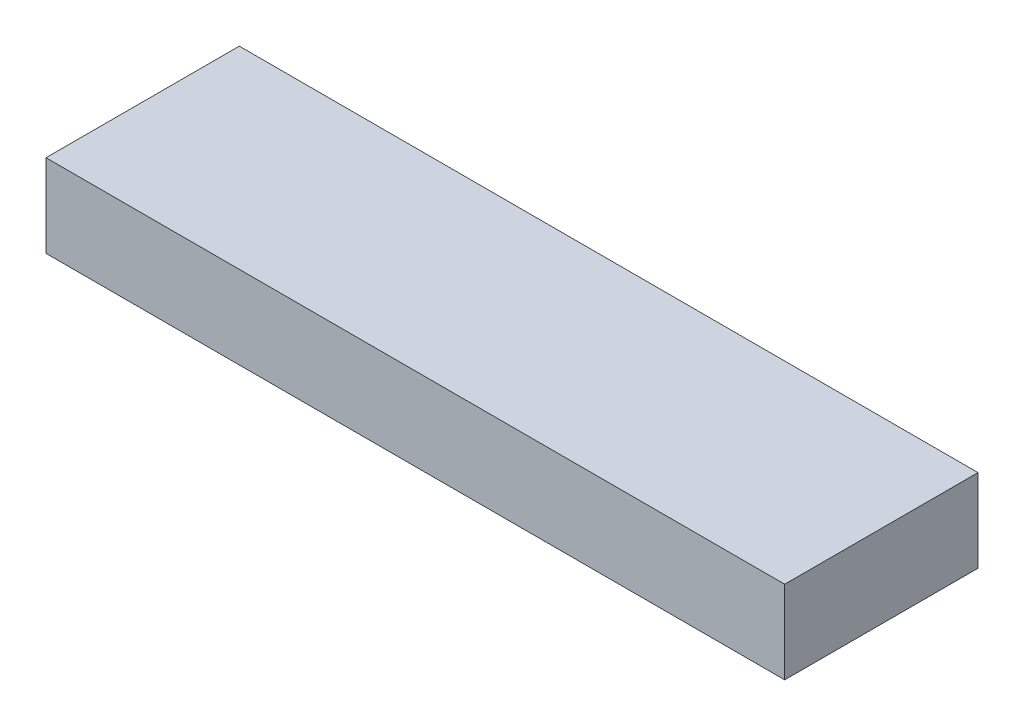
SolidWorks part; units mm, degrees
material "Pine"
ref_plane "Front Plane" through (0, 0, 0) normal (0, 0, 1) x (1, 0, 0)
ref_plane "Top Plane" through (0, 0, 0) normal (0, 1, 0) x (1, 0, 0)
ref_plane "Right Plane" through (0, 0, 0) normal (1, 0, 0) x (0, 0, -1)
sketch "Sketch1" plane through (0, 0, 0) normal (0, 1, 0) x (1, 0, 0)
  line L1 (0, 0) -> (339.725, 0)
  line L2 (0, 0) -> (0, 88.9)
  line L3 (0, 88.9) -> (339.725, 88.9)
  line L4 (339.725, 0) -> (339.725, 88.9)
  dimension "D1" = 88.9
  dimension "D2" = 339.725
extrude "Boss-Extrude1" add sketch "Sketch1" along normal blind 38.1
